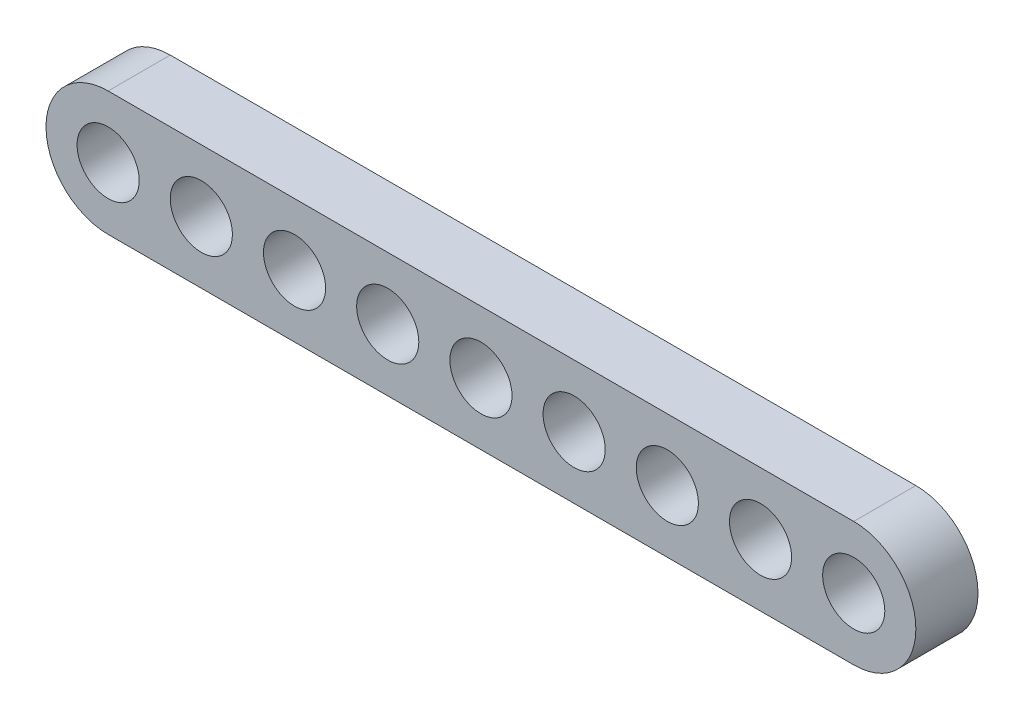
SolidWorks part; units mm, degrees
material "Nylon 101"
ref_plane "Front Plane" through (0, 0, 0) normal (0, 0, 1) x (1, 0, 0)
ref_plane "Top Plane" through (0, 0, 0) normal (0, 1, 0) x (1, 0, 0)
ref_plane "Right Plane" through (0, 0, 0) normal (1, 0, 0) x (0, 0, -1)
sketch "Sketch1" plane through (0, 0, 0) normal (0, 0, 1) x (1, 0, 0)
  line L0 (-60, 0) -> (60, 0) construction
  line L1 (-60, 10) -> (60, 10)
  line L2 (-60, -10) -> (60, -10)
  arc A0 (-60, 10) -> (-60, -10) centre (-60, 0) ccw
  arc A1 (60, -10) -> (60, 10) centre (60, 0) ccw
  circle A2 centre (-60, 0) radius 5
  circle A3 centre (-45, 0) radius 5
  circle A4 centre (-30, 0) radius 5
  circle A5 centre (-15, 0) radius 5
  circle A6 centre (0, 0) radius 5
  circle A7 centre (15, 0) radius 5
  circle A8 centre (30, 0) radius 5
  circle A9 centre (45, 0) radius 5
  circle A10 centre (60, 0) radius 5
  point P2 (0, 0)
  dimension "D3" = 10
  dimension "D1" = 120
  dimension "D2" = 20
extrude "Boss-Extrude1" add sketch "Sketch1" along normal blind 10
